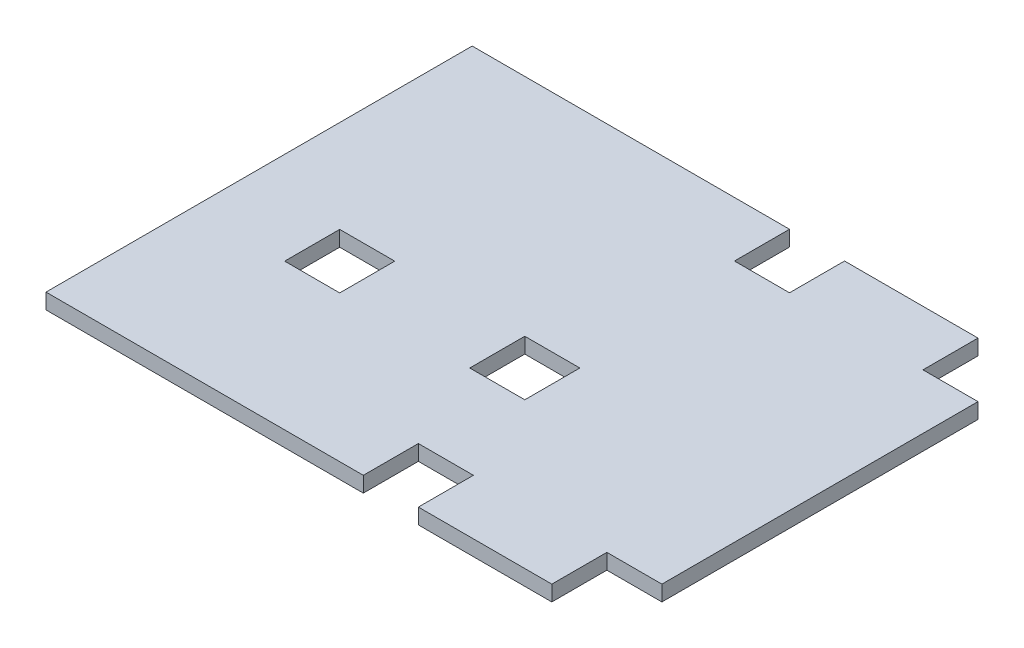
SolidWorks part; units mm, degrees
ref_plane "Front Plane" through (0, 0, 0) normal (0, 0, 1) x (1, 0, 0)
ref_plane "Top Plane" through (0, 0, 0) normal (0, 1, 0) x (1, 0, 0)
ref_plane "Right Plane" through (0, 0, 0) normal (1, 0, 0) x (0, 0, -1)
sketch "Sketch1" plane through (0, 0, 0) normal (0, 1, 0) x (1, 0, 0)
  line L0 (-11.3, -163.7) -> (-11.3, -11.3) construction
  line L1 (-230.3, 0) -> (0, 0)
  line L2 (-230.3, 0) -> (-230.3, -175)
  line L3 (-230.3, -175) -> (0, -175)
  line L4 (0, 0) -> (0, -175)
  line L5 (-77.4, -163.7) -> (-100, -163.7) construction
  line L6 (-77.4, -152.4) -> (-100, -152.4)
  line L7 (-77.4, -152.4) -> (-77.4, -175)
  line L8 (-77.4, -175) -> (-100, -175)
  line L9 (-100, -152.4) -> (-100, -175)
  line L10 (-88.7, -152.4) -> (-88.7, -175) construction
  line L11 (-169.7, -103.7) -> (-192.3, -103.7) construction
  line L12 (-169.7, -92.4) -> (-192.3, -92.4)
  line L13 (-169.7, -92.4) -> (-169.7, -115)
  line L14 (-169.7, -115) -> (-192.3, -115)
  line L15 (-192.3, -92.4) -> (-192.3, -115)
  line L16 (-181, -92.4) -> (-181, -115) construction
  line L17 (0, -11.3) -> (-22.6, -11.3) construction
  line L18 (0, 0) -> (-22.6, 0)
  line L19 (0, 0) -> (0, -22.6)
  line L20 (0, -22.6) -> (-22.6, -22.6)
  line L21 (-22.6, 0) -> (-22.6, -22.6)
  line L22 (-11.3, 0) -> (-11.3, -22.6) construction
  line L23 (0, -163.7) -> (-22.6, -163.7) construction
  line L24 (0, -152.4) -> (-22.6, -152.4)
  line L25 (0, -152.4) -> (0, -175)
  line L26 (0, -175) -> (-22.6, -175)
  line L27 (-22.6, -152.4) -> (-22.6, -175)
  line L28 (-11.3, -152.4) -> (-11.3, -175) construction
  line L29 (-77.4, -11.3) -> (-100, -11.3) construction
  line L30 (-77.4, 0) -> (-100, 0)
  line L31 (-77.4, 0) -> (-77.4, -22.6)
  line L32 (-77.4, -22.6) -> (-100, -22.6)
  line L33 (-100, 0) -> (-100, -22.6)
  line L34 (-88.7, 0) -> (-88.7, -22.6) construction
  line L35 (-93.7, -103.7) -> (-116.3, -103.7) construction
  line L36 (-93.7, -92.4) -> (-116.3, -92.4)
  line L37 (-93.7, -92.4) -> (-93.7, -115)
  line L38 (-93.7, -115) -> (-116.3, -115)
  line L39 (-116.3, -92.4) -> (-116.3, -115)
  line L40 (-105, -92.4) -> (-105, -115) construction
  circle A0 centre (-88.7, -163.7) radius 3.5
  circle A1 centre (-11.3, -163.7) radius 3.5
  circle A2 centre (-11.3, -11.3) radius 3.5
  circle A3 centre (-88.7, -11.3) radius 3.5
  circle A4 centre (-105, -103.7) radius 2.75
  circle A5 centre (-181, -103.7) radius 2.75
  point P13 (-11.3, -87.5)
  point P14 (0, -87.5)
  point P67 (-11.3, -11.3)
  point P68 (-88.7, -11.3)
  point P69 (-105, -103.7)
  point P70 (-11.3, -163.7)
  point P71 (-88.7, -163.7)
  point P72 (-181, -103.7)
  dimension "D3" = 7
  dimension "D4" = 77.4
  dimension "D5" = 152.4
  dimension "D7" = 5.5
  dimension "D1" = 175
  dimension "D2" = 49.3
  dimension "D6" = 11.3
  dimension "D8" = 60
  dimension "D9" = 16.3
  dimension "D10" = 76
  dimension "D11" = 22.6
  dimension "D12" = 22.6
  dimension "D13" = 22.6
  dimension "D14" = 22.6
  dimension "D15" = 22.6
  dimension "D16" = 22.6
  dimension "D17" = 22.6
  dimension "D18" = 22.6
  dimension "D19" = 22.6
  dimension "D20" = 22.6
  dimension "D21" = 22.6
  dimension "D22" = 22.6
extrude "Boss-Extrude1" add sketch "Sketch1" along normal blind 6.35 contours L33 L1 L2 L3 L9 L6 L7 L27 L24 L4 L20 L21 L31 L32 L39 L36 L37 L38 L15 L12 L13 L14
